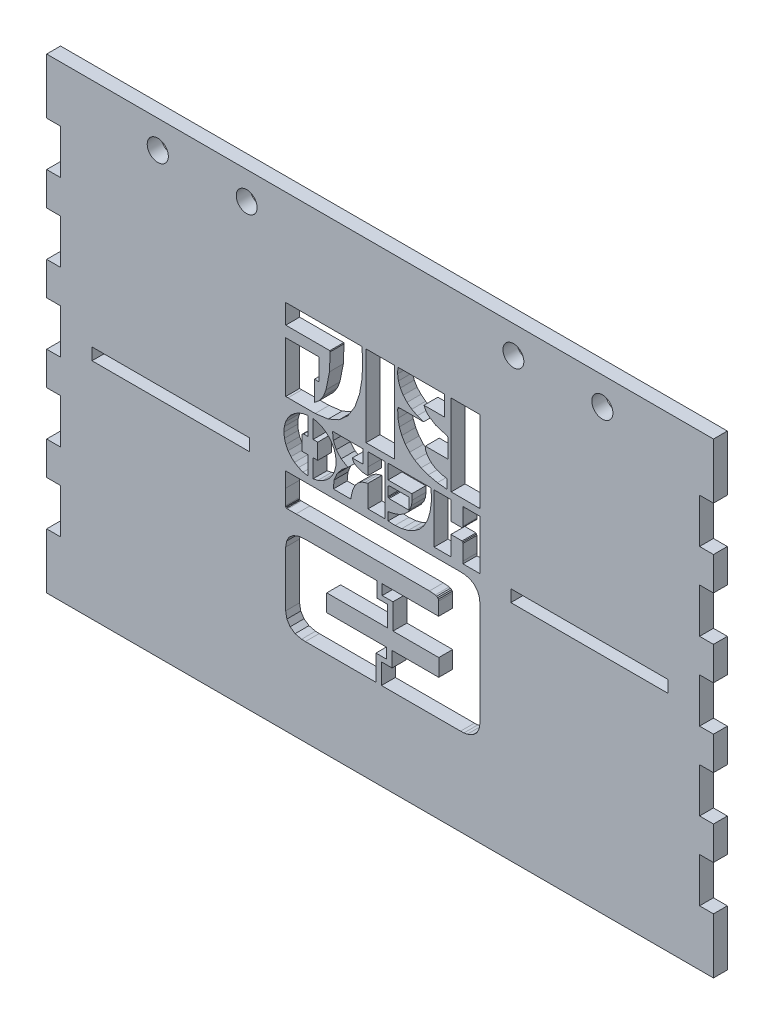
SolidWorks part; units mm, degrees
ref_plane "Front Plane" through (0, 0, 0) normal (0, 0, 1) x (1, 0, 0)
ref_plane "Top Plane" through (0, 0, 0) normal (0, 1, 0) x (1, 0, 0)
ref_plane "Right Plane" through (0, 0, 0) normal (1, 0, 0) x (0, 0, -1)
sketch "Sketch1" plane through (0, 0, 0) normal (0, 0, 1) x (1, 0, 0)
  line L0 (-83.4402, 53.069) -> (-83.4402, 40.369) construction
  line L1 (-83.4402, 53.069) -> (68.9598, 53.069)
  line L2 (-83.4402, 53.069) -> (-83.4402, -53.611)
  line L3 (-83.4402, -53.611) -> (68.9598, -53.611)
  line L4 (68.9598, 53.069) -> (68.9598, -53.611)
  line L5 (-83.4402, 46.719) -> (-58.0402, 46.719) construction
  line L6 (-7.2402, 53.069) -> (-7.2402, -53.611) construction
  line L7 (-47.8802, 46.719) -> (-37.7202, 46.719) construction
  line L8 (-55.6272, 46.719) -> (-47.8802, 46.719) construction
  line L9 (41.1468, 46.719) -> (33.3998, 46.719) construction
  line L10 (33.3998, 46.719) -> (23.2398, 46.719) construction
  line L11 (68.9598, 46.719) -> (43.5598, 46.719) construction
  line L12 (68.9598, -0.271) -> (-83.4402, -0.271) construction
  circle A0 centre (-58.0402, 46.719) radius 2.413
  circle A2 centre (-37.7202, 46.719) radius 2.3847
  circle A3 centre (23.2398, 46.719) radius 2.3847
  circle A5 centre (43.5598, 46.719) radius 2.413
  dimension "D4" = 4.826
  dimension "D7" = 10.16
  dimension "D8" = 4.7693
  dimension "D1" = 106.68
  dimension "D2" = 152.4
  dimension "D3" = 12.7
  dimension "D5" = 25.4
  dimension "D6" = 7.747
extrude "Boss-Extrude1" add sketch "Sketch1" along normal blind 3.175
sketch "Sketch2" plane through (0, 0, 3.175) normal (0, 0, 1) x (1, 0, 0)
  line L0 (-83.4402, 53.069) -> (-83.4402, -53.611) construction
  line L1 (-83.4402, 40.369) -> (-80.2652, 40.369)
  line L2 (-83.4402, 40.369) -> (-83.4402, 30.209)
  line L3 (-83.4402, 30.209) -> (-80.2652, 30.209)
  line L4 (-80.2652, 40.369) -> (-80.2652, 30.209)
  line L5 (-83.4402, 40.369) -> (-83.4402, 53.069) construction
  line L6 (-83.4402, 30.209) -> (-83.4402, -53.611) construction
  dimension "D1" = 3.175
  dimension "D2" = 12.7
  dimension "D3" = 10.16
extrude "Cut-Extrude1" cut sketch "Sketch2" against normal through all contours L4 L3 L2 L1
pattern_linear "LPattern1" count 5 spacing 17.78 along (0, -1, 0) of "Cut-Extrude1"
ref_plane "Plane1" through (-7.2402, 0, 0) normal (-1, 0, 0) x (0, 0, 1)
mirror "Mirror1" about plane through (-7.2402, 0, 0) normal (-1, 0, 0) of "LPattern1", "Cut-Extrude1"
sketch "Sketch3" plane through (0, 0.4582, 0) normal (0, 0, -1) x (-1, 0, 0)
  line L1 (5.7212, -25.9557) -> (19.4226, -25.9557)
  line L2 (19.4226, -25.9557) -> (19.4226, -22.0279)
  line L3 (19.4226, -22.0279) -> (5.5624, -22.0279)
  line L4 (4.2763, -22.0279) -> (-6.1814, -22.0279)
  line L5 (-6.1814, -22.0279) -> (-6.1814, -25.9557)
  line L6 (-6.1814, -25.9557) -> (4.4859, -25.9557)
  line L7 (7.9758, -13.8809) -> (24.4656, -13.8834)
  line L8 (24.4656, -13.8834) -> (25.8576, -14.0353)
  line L9 (25.8576, -14.0353) -> (27.0973, -14.5196)
  line L10 (27.0973, -14.5196) -> (28.0199, -15.2998)
  line L11 (28.0199, -15.2998) -> (28.5992, -16.3545)
  line L12 (28.5992, -16.3545) -> (28.8069, -17.6674)
  line L13 (28.8069, -17.6674) -> (28.8075, -30.2948)
  line L14 (28.8075, -30.2948) -> (28.5352, -31.7712)
  line L15 (28.5352, -31.7712) -> (27.7931, -32.9315)
  line L16 (27.7931, -32.9315) -> (26.6495, -33.719)
  line L17 (26.6495, -33.719) -> (25.1725, -34.0806)
  line L18 (25.1725, -34.0806) -> (24.3105, -34.1116)
  line L19 (24.3105, -34.1116) -> (8.2041, -34.1128)
  line L20 (-9.0177, 30.7644) -> (-9.0177, 12.1727)
  line L21 (6.918, -34.1128) -> (-11.1652, -34.1066)
  line L22 (-11.1652, -34.1066) -> (-11.9354, -34.0682)
  line L23 (-11.9354, -34.0682) -> (-12.6926, -33.941)
  line L24 (-12.6926, -33.941) -> (-13.9266, -33.4425)
  line L25 (-13.9266, -33.4425) -> (-14.8326, -32.6363)
  line L26 (-14.8326, -32.6363) -> (-15.3963, -31.5418)
  line L27 (-15.3963, -31.5418) -> (-15.6028, -30.1782)
  line L28 (-15.6028, -30.1782) -> (-15.6034, -25.4541)
  line L29 (-15.6034, -25.4541) -> (-15.6059, -7.0123)
  line L30 (-15.6059, -7.0123) -> (-15.4781, -5.5254)
  line L31 (-15.4781, -5.5254) -> (-15.0428, -4.3992)
  line L32 (-15.0428, -4.3992) -> (-14.2919, -3.5205)
  line L33 (-14.2919, -3.5205) -> (-13.268, -2.9203)
  line L34 (-13.268, -2.9203) -> (-12.0142, -2.6288)
  line L35 (-12.0142, -2.6288) -> (-11.1076, -2.5836)
  line L36 (-11.1076, -2.5836) -> (28.1378, -2.5823)
  line L37 (28.1378, -2.5823) -> (28.8218, -2.5823)
  line L38 (28.8218, -2.5823) -> (28.8218, -6.0264)
  line L39 (28.8218, -6.0264) -> (28.8286, -9.4781)
  line L40 (28.8286, -9.4781) -> (28.8094, -9.6913)
  line L41 (28.8094, -9.6913) -> (28.7375, -9.8285)
  line L42 (28.7375, -9.8285) -> (28.6009, -9.8984)
  line L43 (28.6009, -9.8984) -> (28.3895, -9.914)
  line L44 (28.3895, -9.914) -> (26.4362, -9.9072)
  line L45 (26.4362, -9.9072) -> (-4.0426, -9.9114)
  line L46 (-4.0426, -9.9114) -> (-5.3938, -10.0293)
  line L47 (-5.3938, -10.0293) -> (-5.6964, -10.1272)
  line L48 (-5.6964, -10.1272) -> (-5.9326, -10.3009)
  line L49 (-5.9326, -10.3009) -> (-6.0883, -10.549)
  line L50 (-6.0883, -10.549) -> (-6.1472, -10.8702)
  line L51 (-6.1472, -10.8702) -> (-6.1522, -13.8845)
  line L52 (-6.1522, -13.8845) -> (-5.6499, -13.8845)
  line L53 (-5.6499, -13.8845) -> (6.7723, -13.8815)
  line L54 (7.2402, 52.6108) -> (7.2402, -54.0692) construction
  line L55 (-8.0057, 14.3643) -> (-7.0612, 14.4883)
  line L56 (-7.0612, 14.4883) -> (-6.1528, 14.7505)
  line L57 (-6.1528, 14.7505) -> (-5.31, 15.1356)
  line L58 (-5.31, 15.1356) -> (-4.5629, 15.6249)
  line L59 (-4.5629, 15.6249) -> (-3.9403, 16.2016)
  line L60 (-3.9403, 16.2016) -> (-3.4714, 16.8484)
  line L61 (-3.4714, 16.8484) -> (-3.1861, 17.548)
  line L62 (-3.1861, 17.548) -> (-3.113, 18.2822)
  line L63 (-3.113, 18.2822) -> (-8.2829, 18.2822)
  line L64 (-8.2829, 18.2822) -> (-8.2829, 22.0016)
  line L65 (-8.2829, 22.0016) -> (-8.2698, 22.4927)
  line L66 (-8.2698, 22.4927) -> (-8.18, 22.7569)
  line L67 (-8.18, 22.7569) -> (-7.9369, 22.8928)
  line L68 (-7.9369, 22.8928) -> (-7.4656, 22.9976)
  line L69 (-7.4656, 22.9976) -> (-5.4539, 23.6027)
  line L70 (-5.4539, 23.6027) -> (-3.7057, 24.768)
  line L71 (-3.7057, 24.768) -> (-3.1627, 25.4253)
  line L72 (-3.1627, 25.4253) -> (-2.7967, 26.2147)
  line L73 (-2.7967, 26.2147) -> (-7.4749, 26.2147)
  line L74 (-7.4756, 30.7644) -> (3.1606, 30.7644)
  line L75 (3.1606, 30.7644) -> (3.2277, 29.4052)
  line L76 (3.2277, 29.4052) -> (3.0367, 28.1159)
  line L77 (3.0367, 28.1159) -> (2.602, 26.9153)
  line L78 (2.602, 26.9153) -> (1.9384, 25.8216)
  line L79 (1.9384, 25.8216) -> (1.0616, 24.8535)
  line L80 (1.0616, 24.8535) -> (-0.0149, 24.0295)
  line L81 (-0.0149, 24.0295) -> (-1.2756, 23.3678)
  line L82 (-1.2756, 23.3678) -> (-2.7063, 22.8865)
  line L83 (-2.7063, 22.8865) -> (-2.2447, 22.8865)
  line L84 (-2.2447, 22.8865) -> (2.6584, 22.8959)
  line L85 (2.6584, 22.8959) -> (2.9214, 22.8716)
  line L86 (2.9214, 22.8716) -> (3.0881, 22.78)
  line L87 (3.0881, 22.78) -> (3.1781, 22.6124)
  line L88 (3.1781, 22.6124) -> (3.211, 22.3568)
  line L89 (3.211, 22.3568) -> (3.1434, 20.6789)
  line L90 (3.1434, 20.6789) -> (2.8297, 19.1187)
  line L91 (2.8297, 19.1187) -> (2.2771, 17.688)
  line L92 (2.2771, 17.688) -> (1.495, 16.3988)
  line L93 (1.495, 16.3988) -> (0.4917, 15.2635)
  line L94 (0.4917, 15.2635) -> (-0.7236, 14.2936)
  line L95 (-0.7236, 14.2936) -> (-2.1431, 13.5017)
  line L96 (-2.1431, 13.5017) -> (-3.7574, 12.8988)
  line L97 (-3.7574, 12.8988) -> (-5.8644, 12.4252)
  line L98 (-5.8644, 12.4252) -> (-8.0057, 12.2032)
  line L99 (-58.5963, -0.1731) -> (-22.6521, -0.1731)
  line L100 (-9.0177, 12.1727) -> (-15.2164, 12.1665)
  line L101 (-15.2164, 12.1665) -> (-15.5743, 12.1857)
  line L102 (-15.5743, 12.1857) -> (-15.5743, 30.7644)
  line L103 (-15.5743, 30.7644) -> (-9.0177, 30.7644)
  line L104 (28.8, 23.7794) -> (28.8, 12.1517)
  line L105 (28.8, 12.1517) -> (28.2811, 12.1517)
  line L106 (28.2811, 12.1517) -> (22.0607, 12.156)
  line L107 (22.0607, 12.156) -> (19.0935, 12.5318)
  line L108 (19.0935, 12.5318) -> (16.5974, 13.6388)
  line L109 (16.5974, 13.6388) -> (14.5659, 15.4661)
  line L110 (14.5659, 15.4661) -> (12.992, 18.0012)
  line L111 (12.992, 18.0012) -> (11.9286, 21.0603)
  line L112 (11.9286, 21.0603) -> (11.3866, 24.2513)
  line L113 (11.3866, 24.2513) -> (11.2068, 27.3762)
  line L114 (11.2068, 27.3762) -> (11.3574, 30.504)
  line L115 (11.3574, 30.504) -> (11.3978, 30.7595)
  line L116 (11.3978, 30.7595) -> (28.7932, 30.7595)
  line L117 (28.7932, 30.7595) -> (28.7932, 26.2674)
  line L118 (28.7932, 26.2674) -> (18.7181, 26.2674)
  line L119 (18.7181, 26.2674) -> (18.6462, 26.059)
  line L120 (18.6462, 26.059) -> (18.8062, 22.0295)
  line L121 (18.8062, 22.0295) -> (19.5858, 18.0738)
  line L122 (19.5858, 18.0738) -> (20.1755, 16.5539)
  line L123 (20.1755, 16.5539) -> (21.097, 15.2088)
  line L124 (21.097, 15.2088) -> (21.6172, 14.7456)
  line L125 (21.6172, 14.7456) -> (22.2399, 14.2544)
  line L126 (22.2399, 14.2544) -> (22.2399, 18.8638)
  line L127 (22.2399, 18.8638) -> (21.1881, 18.8638)
  line L128 (21.1881, 18.8638) -> (21.1881, 23.7794)
  line L129 (21.1881, 23.7794) -> (28.8, 23.7794)
  line L130 (3.9371, 30.7533) -> (10.4434, 30.7533)
  line L131 (10.4434, 30.7533) -> (10.4434, 12.1783)
  line L132 (10.4434, 12.1783) -> (3.9371, 12.1783)
  line L133 (3.9371, 12.1783) -> (3.9371, 30.7533)
  line L134 (10.0286, 7.5801) -> (10.0286, 5.8513)
  line L135 (10.0286, 5.8513) -> (11.2575, 5.9529)
  line L136 (11.2575, 5.9529) -> (12.3875, 6.2934)
  line L137 (12.3875, 6.2934) -> (13.2295, 6.8454)
  line L138 (13.2295, 6.8454) -> (13.5968, 7.5801)
  line L139 (13.5968, 7.5801) -> (11.0945, 7.5801)
  line L140 (11.0815, 10.6193) -> (18.1088, 10.6193)
  line L141 (18.1088, 10.6193) -> (17.9151, 8.8874)
  line L142 (17.9151, 8.8874) -> (17.2448, 7.3817)
  line L143 (17.2448, 7.3817) -> (16.1237, 6.1446)
  line L144 (16.1237, 6.1446) -> (14.5802, 5.2199)
  line L145 (14.5802, 5.2199) -> (16.0108, 4.0716)
  line L146 (16.0108, 4.0716) -> (17.0873, 2.7258)
  line L147 (17.0873, 2.7258) -> (17.7447, 1.1434)
  line L148 (17.7447, 1.1434) -> (17.9207, -0.717)
  line L149 (17.9207, -0.717) -> (13.9471, -0.717)
  line L150 (13.9471, -0.717) -> (13.7542, 0.2151)
  line L151 (13.7542, 0.2151) -> (13.5272, 1.1315)
  line L152 (13.5272, 1.1315) -> (13.1998, 1.9905)
  line L153 (13.1998, 1.9905) -> (12.7503, 2.7593)
  line L154 (12.7503, 2.7593) -> (12.1494, 3.4104)
  line L155 (12.1494, 3.4104) -> (11.368, 3.9147)
  line L156 (11.368, 3.9147) -> (10.7324, 4.1467)
  line L157 (10.7324, 4.1467) -> (10.0148, 4.3581)
  line L158 (10.0148, 4.3581) -> (10.0148, -0.7134)
  line L159 (10.0148, -0.7134) -> (6.1361, -0.7134)
  line L160 (6.1361, -0.7134) -> (6.1361, 10.6193)
  line L161 (6.1361, 10.6193) -> (10.0328, 10.6193)
  line L162 (22.535, 6.7759) -> (22.3626, 6.7759)
  line L163 (22.3626, 6.7759) -> (21.4803, 6.7759)
  line L164 (21.4803, 6.7759) -> (21.4803, 3.1617)
  line L165 (21.4803, 3.1617) -> (22.535, 3.1617)
  line L166 (23.7256, 3.1617) -> (25.0626, 3.1617)
  line L167 (25.0626, 3.1617) -> (25.0472, 6.5364)
  line L168 (25.0472, 6.5364) -> (24.9256, 6.6802)
  line L169 (24.9256, 6.6802) -> (24.7171, 6.7647)
  line L170 (24.7171, 6.7647) -> (23.7256, 6.7777)
  line L171 (23.7256, 10.9337) -> (24.8636, 10.7303)
  line L172 (24.8636, 10.7303) -> (25.9128, 10.3279)
  line L173 (25.9128, 10.3279) -> (26.8524, 9.7456)
  line L174 (26.8524, 9.7456) -> (27.6634, 9.0058)
  line L175 (27.6634, 9.0058) -> (28.3251, 8.1277)
  line L176 (28.3251, 8.1277) -> (28.8181, 7.1324)
  line L177 (28.8181, 7.1324) -> (29.122, 6.0404)
  line L178 (29.122, 6.0404) -> (29.2168, 4.8714)
  line L179 (29.2168, 4.8714) -> (29.094, 3.7249)
  line L180 (29.094, 3.7249) -> (28.7703, 2.6558)
  line L181 (28.7703, 2.6558) -> (28.2662, 1.6847)
  line L182 (28.2662, 1.6847) -> (27.6008, 0.8308)
  line L183 (27.6008, 0.8308) -> (26.7941, 0.1127)
  line L184 (26.7941, 0.1127) -> (25.8663, -0.4492)
  line L185 (25.8663, -0.4492) -> (24.8368, -0.8355)
  line L186 (24.8368, -0.8355) -> (23.7256, -1.0277)
  line L187 (22.5343, -1.0016) -> (21.4455, -0.7641)
  line L188 (21.4455, -0.7641) -> (20.4415, -0.338)
  line L189 (20.4415, -0.338) -> (19.5412, 0.2566)
  line L190 (19.5412, 0.2566) -> (18.7646, 0.9994)
  line L191 (18.7646, 0.9994) -> (18.1309, 1.8708)
  line L192 (18.1309, 1.8708) -> (17.6596, 2.8506)
  line L193 (17.6596, 2.8506) -> (17.3707, 3.9184)
  line L194 (17.3707, 3.9184) -> (17.2826, 5.0543)
  line L195 (17.2826, 5.0543) -> (17.4035, 6.1588)
  line L196 (17.4035, 6.1588) -> (17.7174, 7.1951)
  line L197 (17.7174, 7.1951) -> (18.2028, 8.1444)
  line L198 (18.2028, 8.1444) -> (18.8417, 8.9878)
  line L199 (18.8417, 8.9878) -> (19.6136, 9.7053)
  line L200 (19.6136, 9.7053) -> (20.4998, 10.2788)
  line L201 (20.4998, 10.2788) -> (21.4796, 10.6883)
  line L202 (21.4796, 10.6883) -> (22.535, 10.9145)
  line L203 (-11.7246, -0.7245) -> (-15.5823, -0.7245)
  line L204 (-15.5823, -0.7245) -> (-15.5823, 10.6329)
  line L205 (-15.5823, 10.6329) -> (-11.7605, 10.6329)
  line L206 (-11.7605, 10.6329) -> (-11.7258, 10.1066)
  line L207 (-11.7258, 10.1066) -> (-11.7308, 6.7908)
  line L208 (-11.7308, 6.7908) -> (-11.7146, 6.5706)
  line L209 (-11.7146, 6.5706) -> (-11.6458, 6.42)
  line L210 (-11.6458, 6.42) -> (-11.5063, 6.3356)
  line L211 (-11.5063, 6.3356) -> (-11.2768, 6.3145)
  line L212 (-11.2768, 6.3145) -> (-8.9916, 6.322)
  line L213 (-8.9916, 6.322) -> (-8.9916, 10.628)
  line L214 (-8.9916, 10.628) -> (-5.1098, 10.628)
  line L215 (-5.1098, 10.628) -> (-5.1098, -0.7108)
  line L216 (-5.1098, -0.7108) -> (-8.9663, -0.7108)
  line L217 (-8.9663, -0.7108) -> (-8.9663, 3.7316)
  line L218 (-8.9663, 3.7316) -> (-11.4995, 3.7144)
  line L219 (-11.4995, 3.7144) -> (-11.6359, 3.5692)
  line L220 (-11.6359, 3.5692) -> (-11.7146, 3.3237)
  line L221 (-11.7146, 3.3237) -> (-11.7246, -0.1731)
  line L222 (-11.7246, -0.1731) -> (-11.7246, -0.7245)
  line L223 (-0.0292, 7.3141) -> (-0.1016, 6.0771)
  line L224 (-0.1016, 6.0771) -> (0.0503, 4.9596)
  line L225 (0.0503, 4.9596) -> (0.4218, 3.9685)
  line L226 (0.4218, 3.9685) -> (1.0083, 3.1079)
  line L227 (1.0083, 3.1079) -> (1.8044, 2.3829)
  line L228 (1.8044, 2.3829) -> (2.8061, 1.7982)
  line L229 (2.8061, 1.7982) -> (4.0071, 1.3585)
  line L230 (4.0071, 1.3585) -> (5.4043, 1.0696)
  line L231 (5.4043, 1.0696) -> (5.4043, -0.7927)
  line L232 (5.4043, -0.7927) -> (3.8161, -0.8739)
  line L233 (3.8161, -0.8739) -> (2.2746, -0.74)
  line L234 (2.2746, -0.74) -> (0.8129, -0.3722)
  line L235 (0.8129, -0.3722) -> (-0.5376, 0.2498)
  line L236 (-0.5376, 0.2498) -> (-1.7431, 1.1451)
  line L237 (-1.7431, 1.1451) -> (-2.772, 2.3327)
  line L238 (-2.772, 2.3327) -> (-3.5905, 3.8334)
  line L239 (-3.5905, 3.8334) -> (-4.166, 5.6652)
  line L240 (-4.166, 5.6652) -> (-4.4878, 7.9775)
  line L241 (-4.4878, 7.9775) -> (-4.4474, 10.3129)
  line L242 (-4.4474, 10.3129) -> (-4.3618, 10.5784)
  line L243 (-4.3618, 10.5784) -> (-4.0971, 10.6634)
  line L244 (-4.0971, 10.6634) -> (5.2133, 10.6558)
  line L245 (5.2133, 10.6558) -> (5.4118, 10.6132)
  line L246 (5.4118, 10.6132) -> (5.4118, 7.3141)
  line L247 (5.4118, 7.3141) -> (-0.0292, 7.3141)
  line L248 (0.6635, 6.3195) -> (5.1538, 6.3065)
  line L249 (5.1538, 6.3065) -> (5.3268, 6.201)
  line L250 (5.3268, 6.201) -> (5.4303, 6.0188)
  line L251 (5.4303, 6.0188) -> (5.431, 4.0225)
  line L252 (5.431, 4.0225) -> (5.3367, 3.852)
  line L253 (5.3367, 3.852) -> (5.1779, 3.7521)
  line L254 (5.1779, 3.7521) -> (0.6635, 3.7404)
  line L255 (0.6635, 3.7404) -> (0.6635, 6.3195)
  line L256 (-58.5963, -0.1731) -> (-58.5963, -2.9203)
  line L257 (22.535, 6.7759) -> (22.535, 10.9145)
  line L258 (23.7256, 6.7777) -> (23.7256, 10.9337)
  line L259 (22.5343, -1.0016) -> (22.535, 3.1617)
  line L260 (23.7256, -1.0277) -> (23.7256, 3.1617)
  line L261 (10.0286, 7.5801) -> (10.0328, 10.6193)
  line L262 (11.0945, 7.5801) -> (11.0815, 10.6193)
  line L263 (4.4859, -25.9557) -> (4.4908, -29.4334)
  line L264 (4.4908, -29.4334) -> (6.9515, -29.4334)
  line L265 (6.9515, -29.4334) -> (6.918, -34.1128)
  line L266 (5.7212, -25.9557) -> (5.7212, -28.3222)
  line L267 (5.7212, -28.3222) -> (8.1818, -28.3222)
  line L268 (8.1818, -28.3222) -> (8.2041, -34.1128)
  line L269 (7.9758, -13.8809) -> (7.9901, -17.3486)
  line L270 (7.9901, -17.3486) -> (5.5295, -17.3486)
  line L271 (5.5295, -17.3486) -> (5.5624, -22.0279)
  line L272 (6.7723, -13.8815) -> (6.7592, -16.2367)
  line L273 (6.7592, -16.2367) -> (4.2993, -16.2374)
  line L274 (4.2993, -16.2374) -> (4.2763, -22.0279)
  line L275 (-58.5963, -2.9203) -> (-22.6521, -2.9203)
  line L276 (-22.6521, -0.1731) -> (-22.6521, -2.9203)
  line L277 (-7.4749, 26.2147) -> (-7.4756, 30.7644)
  line L278 (-68.9598, 52.6108) -> (83.4402, 52.6108) construction
  line L279 (-8.0057, 14.3643) -> (-8.0057, 12.2032)
  line L280 (83.4402, -54.0692) -> (-68.9598, -54.0692) construction
  line L281 (37.1325, -0.1731) -> (37.1325, -2.9203)
  line L282 (73.0766, -2.9203) -> (37.1325, -2.9203)
  line L283 (73.0766, -0.1731) -> (73.0766, -2.9203)
  line L284 (73.0766, -0.1731) -> (37.1325, -0.1731)
extrude "Cut-Extrude2" cut sketch "Sketch3" against normal up to next
